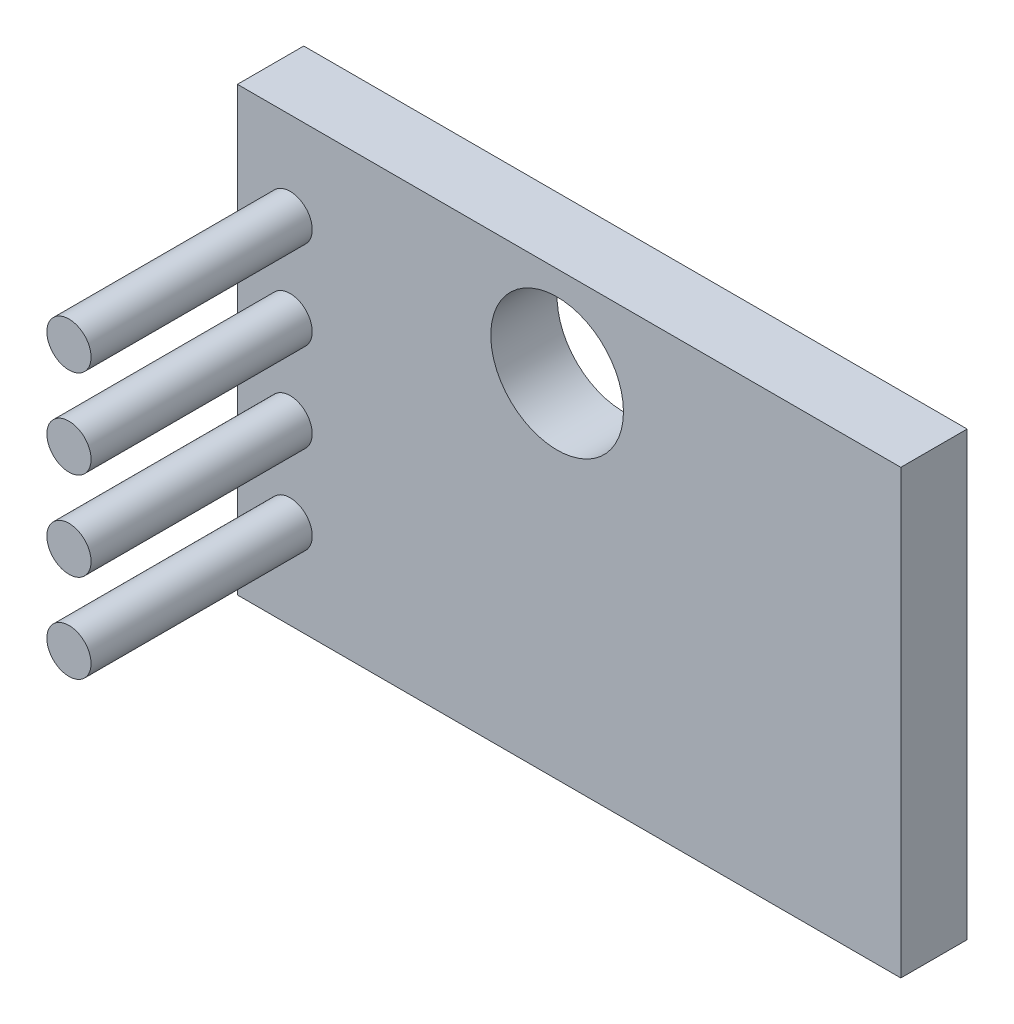
SolidWorks part; units mm, degrees
ref_plane "Front Plane" through (0, 0, 0) normal (0, 0, 1) x (1, 0, 0)
ref_plane "Top Plane" through (0, 0, 0) normal (0, 1, 0) x (1, 0, 0)
ref_plane "Right Plane" through (0, 0, 0) normal (1, 0, 0) x (0, 0, -1)
sketch "Sketch1" plane through (0, 0, 0) normal (0, 0, 1) x (1, 0, 0)
  line L1 (156.5831, 62.5911) -> (171.5831, 62.5911)
  line L2 (156.5831, 62.5911) -> (156.5831, 72.5911)
  line L3 (156.5831, 72.5911) -> (171.5831, 72.5911)
  line L4 (171.5831, 62.5911) -> (171.5831, 72.5911)
  circle A0 centre (163.8117, 70.5429) radius 1.5
extrude "Boss-Extrude1" add sketch "Sketch1" along normal blind 1.5
sketch "Sketch2" plane through (0, 0, 1.5) normal (0, 0, 1) x (1, 0, 0)
  line L0 (156.5831, 67.5911) -> (160.5532, 67.5911) construction
  line L1 (156.5831, 72.5911) -> (156.5831, 62.5911) construction
  circle A0 centre (157.7742, 68.5911) radius 0.5
  circle A1 centre (157.7742, 70.5911) radius 0.5
  circle A2 centre (157.7742, 64.5911) radius 0.5
  circle A3 centre (157.7742, 66.5911) radius 0.5
extrude "Boss-Extrude2" add sketch "Sketch2" along normal blind 5
